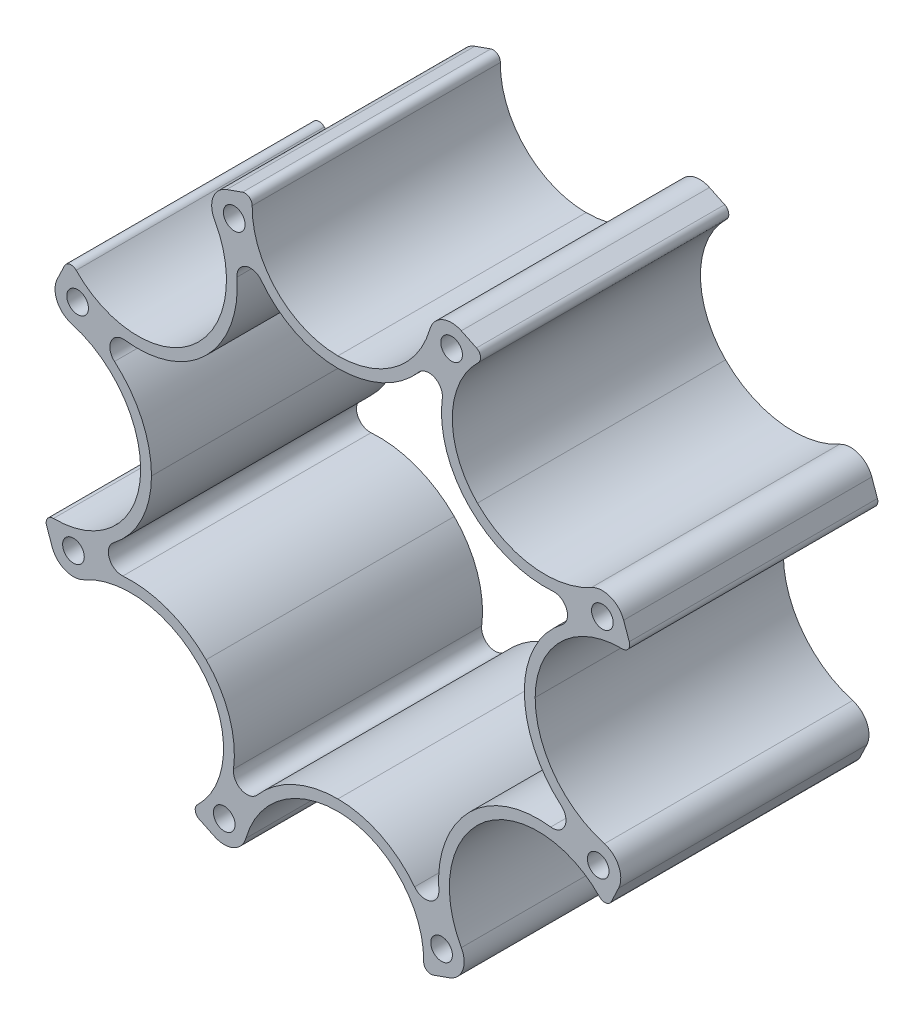
SolidWorks part; units mm, degrees
material "6061-T6 (SS)"
ref_plane "前视基准面" through (0, 0, 0) normal (0, 0, 1) x (1, 0, 0)
ref_plane "上视基准面" through (0, 0, 0) normal (0, 1, 0) x (1, 0, 0)
ref_plane "右视基准面" through (0, 0, 0) normal (1, 0, 0) x (0, 0, -1)
sketch "草图1" plane through (0, 0, 0) normal (0, 0, 1) x (1, 0, 0)
  line L0 (0, 31.3575) -> (0, 0) construction
  line L1 (0, 0) -> (22.1731, 22.1731) construction
  line L4 (0, 31.3575) -> (22.1731, 22.1731) construction
  line L6 (11.6409, 26.5357) -> (12.5976, 28.8454) construction
  line L7 (21.7656, 23.184) -> (15.5687, 29.0018) construction
  line L8 (21.7656, 23.184) -> (27.9942, 29.8184) construction
  line L9 (15.357, 30.2989) -> (13.674, 31.1018)
  line L10 (32.2836, 10.5656) -> (31.6613, 12.3233)
  line L11 (30.2989, -15.357) -> (31.1018, -13.674)
  line L12 (10.5656, -32.2836) -> (12.3233, -31.6613)
  line L13 (-15.357, -30.2989) -> (-13.674, -31.1018)
  line L14 (-32.2836, -10.5656) -> (-31.6613, -12.3233)
  line L15 (-30.2989, 15.357) -> (-31.1018, 13.674)
  line L16 (-10.5656, 32.2836) -> (-12.3233, 31.6613)
  circle A0 centre (0, 0) radius 31.3575 construction
  arc A9 (15.5687, 29.0018) -> (15.4556, 15.4556) centre (22.1731, 22.1731) ccw
  circle A11 centre (12.5976, 28.8454) radius 1.2
  circle A13 centre (0, 0) radius 40.9 construction
  arc A16 (15.5687, 29.0018) -> (15.357, 30.2989) centre (15.0125, 29.5769) ccw
  arc A17 (13.674, 31.1018) -> (10.1948, 29.5357) centre (12.5976, 28.8454) ccw
  arc A18 (0, 21.8575) -> (10.1948, 29.5357) centre (0, 32.4647) ccw
  arc A19 (31.5161, 9.4987) -> (21.8575, 0) centre (31.3575, 0) ccw
  arc A20 (31.5161, 9.4987) -> (32.2836, 10.5656) centre (31.5295, 10.2986) ccw
  arc A21 (31.6613, 12.3233) -> (28.0937, 13.6761) centre (29.3046, 11.4889) ccw
  arc A22 (15.4556, 15.4556) -> (28.0937, 13.6761) centre (22.956, 22.956) ccw
  circle A23 centre (29.3046, 11.4889) radius 1.2
  arc A24 (29.0018, -15.5687) -> (15.4556, -15.4556) centre (22.1731, -22.1731) ccw
  arc A25 (29.0018, -15.5687) -> (30.2989, -15.357) centre (29.5769, -15.0125) ccw
  arc A26 (31.1018, -13.674) -> (29.5357, -10.1948) centre (28.8454, -12.5976) ccw
  arc A27 (21.8575, 0) -> (29.5357, -10.1948) centre (32.4647, 0) ccw
  circle A28 centre (28.8454, -12.5976) radius 1.2
  arc A29 (9.4987, -31.5161) -> (0, -21.8575) centre (0, -31.3575) ccw
  arc A30 (9.4987, -31.5161) -> (10.5656, -32.2836) centre (10.2986, -31.5295) ccw
  arc A31 (12.3233, -31.6613) -> (13.6761, -28.0937) centre (11.4889, -29.3046) ccw
  arc A32 (15.4556, -15.4556) -> (13.6761, -28.0937) centre (22.956, -22.956) ccw
  circle A33 centre (11.4889, -29.3046) radius 1.2
  arc A34 (-15.5687, -29.0018) -> (-15.4556, -15.4556) centre (-22.1731, -22.1731) ccw
  arc A35 (-15.5687, -29.0018) -> (-15.357, -30.2989) centre (-15.0125, -29.5769) ccw
  arc A36 (-13.674, -31.1018) -> (-10.1948, -29.5357) centre (-12.5976, -28.8454) ccw
  arc A37 (0, -21.8575) -> (-10.1948, -29.5357) centre (0, -32.4647) ccw
  circle A38 centre (-12.5976, -28.8454) radius 1.2
  arc A39 (-31.5161, -9.4987) -> (-21.8575, 0) centre (-31.3575, 0) ccw
  arc A40 (-31.5161, -9.4987) -> (-32.2836, -10.5656) centre (-31.5295, -10.2986) ccw
  arc A41 (-31.6613, -12.3233) -> (-28.0937, -13.6761) centre (-29.3046, -11.4889) ccw
  arc A42 (-15.4556, -15.4556) -> (-28.0937, -13.6761) centre (-22.956, -22.956) ccw
  circle A43 centre (-29.3046, -11.4889) radius 1.2
  arc A44 (-29.0018, 15.5687) -> (-15.4556, 15.4556) centre (-22.1731, 22.1731) ccw
  arc A45 (-29.0018, 15.5687) -> (-30.2989, 15.357) centre (-29.5769, 15.0125) ccw
  arc A46 (-31.1018, 13.674) -> (-29.5357, 10.1948) centre (-28.8454, 12.5976) ccw
  arc A47 (-21.8575, 0) -> (-29.5357, 10.1948) centre (-32.4647, 0) ccw
  circle A48 centre (-28.8454, 12.5976) radius 1.2
  arc A49 (-9.4987, 31.5161) -> (0, 21.8575) centre (0, 31.3575) ccw
  arc A50 (-9.4987, 31.5161) -> (-10.5656, 32.2836) centre (-10.2986, 31.5295) ccw
  arc A51 (-12.3233, 31.6613) -> (-13.6761, 28.0937) centre (-11.4889, 29.3046) ccw
  arc A52 (-15.4556, 15.4556) -> (-13.6761, 28.0937) centre (-22.956, 22.956) ccw
  circle A53 centre (-11.4889, 29.3046) radius 1.2
  point P98 (0, 0)
  dimension "D1" = 9.5
  dimension "D3" = 45
  dimension "D4" = 2.4
  dimension "D5" = 9.1
  dimension "D8" = 81.8
  dimension "D9" = 9.5
  dimension "D10" = 2.5
  dimension "D11" = 0.8
  dimension "D2" = 24
  dimension "D6" = 11.4
  dimension "D7" = 2.5
  dimension "D13" = 8.5
  dimension "D12" = 8
extrude "凸台-拉伸1" add sketch "草图1" along normal blind 27.5
cosmetic thread "装饰螺纹线1" parameters "D2"=3
cosmetic thread "装饰螺纹线2" parameters "D2"=3
cosmetic thread "装饰螺纹线3" parameters "D2"=3
cosmetic thread "装饰螺纹线4" parameters "D2"=3
cosmetic thread "装饰螺纹线5" parameters "D2"=3
cosmetic thread "装饰螺纹线6" parameters "D2"=3
cosmetic thread "装饰螺纹线7" parameters "D2"=3
cosmetic thread "装饰螺纹线8" parameters "D2"=3
sketch "草图2" plane through (0, 0, 0) normal (0, 0, -1) x (-1, 0, 0)
  line L0 (0, 0) -> (21.8575, 0) construction
  line L1 (0, 0) -> (15.4556, -15.4556) construction
  arc A0 (20.6575, 0) -> (24.8509, -8.4944) centre (31.3575, 0) ccw
  arc A1 (23.828, -11.1811) -> (14.6071, -14.6071) centre (22.956, -22.956) ccw
  arc A2 (23.828, -11.1811) -> (24.8509, -8.4944) centre (23.9388, -9.6852) ccw
  arc A4 (28.0937, -13.6761) -> (15.4556, -15.4556) centre (22.956, -22.956) ccw construction
  arc A5 (21.8575, 0) -> (31.5161, -9.4987) centre (31.3575, 0) ccw construction
  arc A6 (14.6071, -14.6071) -> (11.5658, -23.5787) centre (22.1731, -22.1731) ccw
  arc A7 (8.9427, -24.7551) -> (0, -20.6575) centre (0, -32.4647) ccw
  arc A8 (8.9427, -24.7551) -> (11.5658, -23.5787) centre (10.0788, -23.7757) ccw
  arc A9 (0, -20.6575) -> (-8.4944, -24.8509) centre (0, -31.3575) ccw
  arc A10 (-11.1811, -23.828) -> (-14.6071, -14.6071) centre (-22.956, -22.956) ccw
  arc A11 (-11.1811, -23.828) -> (-8.4944, -24.8509) centre (-9.6852, -23.9388) ccw
  arc A12 (-14.6071, -14.6071) -> (-23.5787, -11.5658) centre (-22.1731, -22.1731) ccw
  arc A13 (-24.7551, -8.9427) -> (-20.6575, 0) centre (-32.4647, 0) ccw
  arc A14 (-24.7551, -8.9427) -> (-23.5787, -11.5658) centre (-23.7757, -10.0788) ccw
  arc A15 (-20.6575, 0) -> (-24.8509, 8.4944) centre (-31.3575, 0) ccw
  arc A16 (-23.828, 11.1811) -> (-14.6071, 14.6071) centre (-22.956, 22.956) ccw
  arc A17 (-23.828, 11.1811) -> (-24.8509, 8.4944) centre (-23.9388, 9.6852) ccw
  arc A18 (-14.6071, 14.6071) -> (-11.5658, 23.5787) centre (-22.1731, 22.1731) ccw
  arc A19 (-8.9427, 24.7551) -> (0, 20.6575) centre (0, 32.4647) ccw
  arc A20 (-8.9427, 24.7551) -> (-11.5658, 23.5787) centre (-10.0788, 23.7757) ccw
  arc A21 (0, 20.6575) -> (8.4944, 24.8509) centre (0, 31.3575) ccw
  arc A22 (11.1811, 23.828) -> (14.6071, 14.6071) centre (22.956, 22.956) ccw
  arc A23 (11.1811, 23.828) -> (8.4944, 24.8509) centre (9.6852, 23.9388) ccw
  arc A24 (14.6071, 14.6071) -> (23.5787, 11.5658) centre (22.1731, 22.1731) ccw
  arc A25 (24.7551, 8.9427) -> (20.6575, 0) centre (32.4647, 0) ccw
  arc A26 (24.7551, 8.9427) -> (23.5787, 11.5658) centre (23.7757, 10.0788) ccw
  point P72 (0, 0)
  dimension "D1" = 1.2
  dimension "D2" = 1.2
  dimension "D3" = 1.5
  dimension "D4" = 8
extrude "切除-拉伸1" cut sketch "草图2" against normal through all
